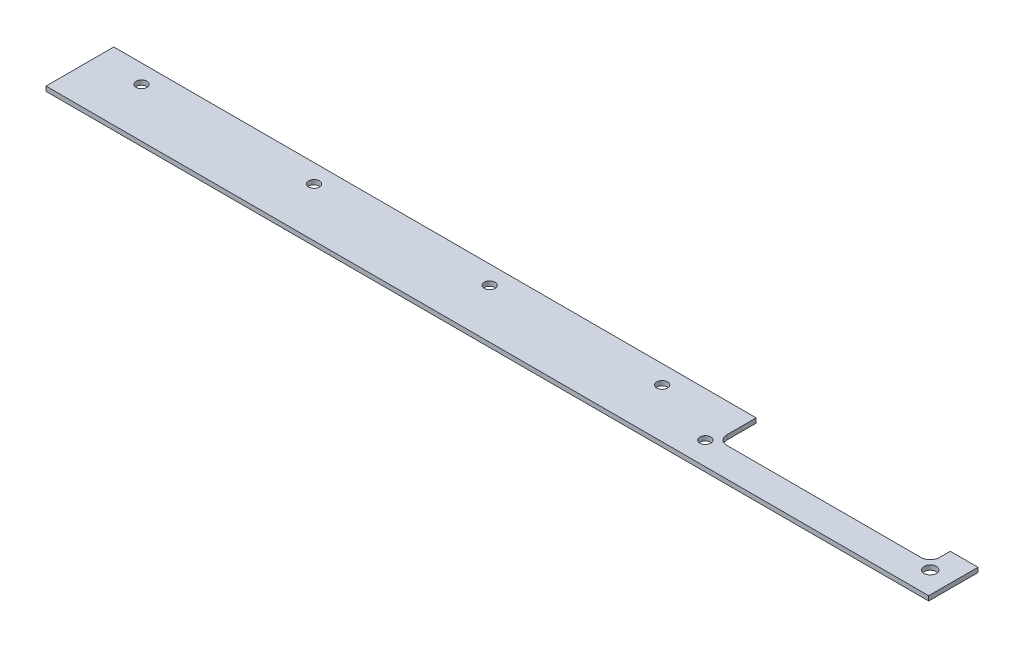
SolidWorks part; units mm, degrees
material "Простая углеродистая сталь"
ref_plane "Спереди" through (0, 0, 0) normal (0, 0, 1) x (1, 0, 0)
ref_plane "Сверху" through (0, 0, 0) normal (0, 1, 0) x (1, 0, 0)
ref_plane "Справа" through (0, 0, 0) normal (1, 0, 0) x (0, 0, -1)
sketch "Эскиз1" plane through (0, 0, 0) normal (0, 1, 0) x (1, 0, 0)
  line L0 (208.5, 22) -> (208.5, 12.5)
  line L1 (0, 0) -> (286.5, 0)
  line L2 (0, 0) -> (0, 22)
  line L3 (0, 22) -> (208.5, 22)
  line L5 (211.5, 9.5) -> (274.5, 9.5)
  line L7 (277.5, 12.5) -> (277.5, 16)
  line L8 (277.5, 16) -> (286.5, 16)
  line L9 (286.5, 16) -> (286.5, 0)
  circle A1 centre (206.5, 7.5) radius 1.75
  circle A2 centre (71, 16) radius 1.75
  circle A3 centre (15, 16) radius 1.75
  circle A4 centre (128, 16) radius 1.75
  circle A5 centre (184, 16) radius 1.75
  circle A8 centre (279.5, 7.5) radius 2
  arc A9 (208.5, 12.5) -> (211.5, 9.5) centre (211.5, 12.5) ccw
  arc A10 (274.5, 9.5) -> (277.5, 12.5) centre (274.5, 12.5) ccw
  dimension "D2" = 3
  dimension "D3" = 3
  dimension "D1" = 2
extrude "Бобышка-Вытянуть1" add sketch "Эскиз1" along normal blind 1.5 contours L2 L1 L3
